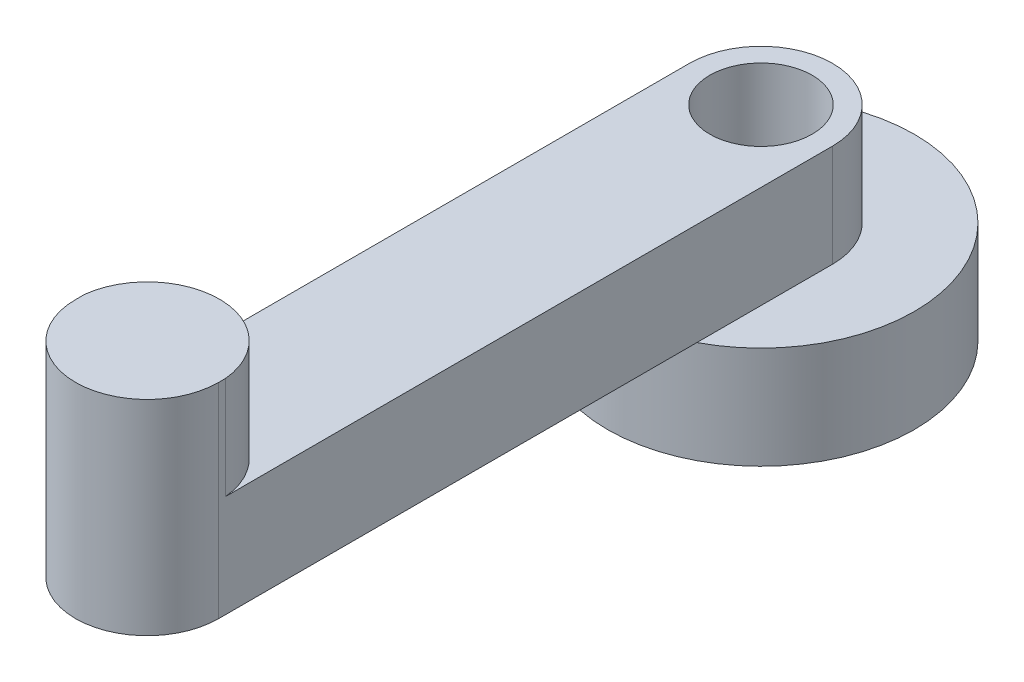
SolidWorks part; units mm, degrees
ref_plane "Front Plane" through (0, 0, 0) normal (0, 0, 1) x (1, 0, 0)
ref_plane "Top Plane" through (0, 0, 0) normal (0, 1, 0) x (1, 0, 0)
ref_plane "Right Plane" through (0, 0, 0) normal (1, 0, 0) x (0, 0, -1)
sketch "Sketch1" plane through (0, 0, 0) normal (0, 1, 0) x (1, 0, 0)
  circle A0 centre (0, 0) radius 75
extrude "Boss-Extrude1" add sketch "Sketch1" along normal blind 50
sketch "Sketch2" plane through (0, 50, 0) normal (0, 1, 0) x (1, 0, 0)
  line L0 (-35, 0) -> (-35, -300)
  line L1 (35, 0) -> (35, -300)
  arc A0 (35, 0) -> (-35, 0) centre (0, 0) ccw
  arc A1 (-35, -300) -> (35, -300) centre (0, -300) ccw
extrude "Boss-Extrude2" add sketch "Sketch2" along normal blind 50
sketch "Sketch3" plane through (0, 100, 0) normal (0, 1, 0) x (1, 0, 0)
  circle A0 centre (35.2238, -301.0378) radius 0.2391
  circle A1 centre (-0.0723, -299.801) radius 35.2117
  line M2 (-35, 0) -> (-35, -300)
  arc M3 (-35, -300) -> (35, -300) centre (0, -300) ccw
  line M4 (35, -300) -> (35, 0)
extrude "Boss-Extrude3" add sketch "Sketch3" along normal blind 50 contours A1 M4 M2 M3
sketch "Sketch4" plane through (0, 0, 0) normal (0, -1, 0) x (1, 0, 0)
  circle A0 centre (0, 0) radius 25
extrude "Cut-Extrude1" cut sketch "Sketch4" against normal through all
